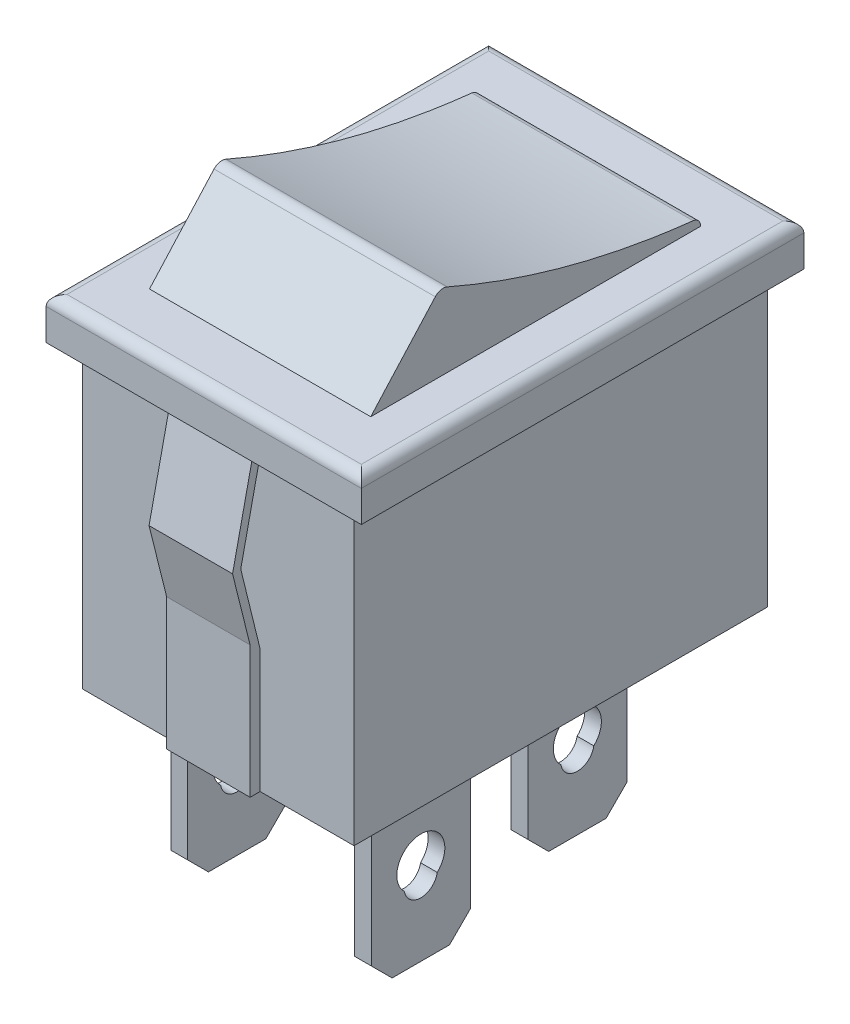
SolidWorks part; units mm, degrees
ref_plane "Front Plane" through (0, 0, 0) normal (0, 0, 1) x (1, 0, 0)
ref_plane "Top Plane" through (0, 0, 0) normal (0, 1, 0) x (1, 0, 0)
ref_plane "Right Plane" through (0, 0, 0) normal (1, 0, 0) x (0, 0, -1)
sketch "Sketch1" plane through (0, 0, 0) normal (0, 1, 0) x (1, 0, 0)
  line L1 (-6.5, -9.9) -> (6.5, -9.9)
  line L2 (-6.5, -9.9) -> (-6.5, 9.9)
  line L3 (-6.5, 9.9) -> (6.5, 9.9)
  line L4 (6.5, -9.9) -> (6.5, 9.9)
  line L5 (-6.5, -9.9) -> (6.5, 9.9) construction
  line L6 (-6.5, 9.9) -> (6.5, -9.9) construction
  point P0 (0, 0)
  dimension "D1" = 13
  dimension "D2" = 19.8
extrude "Boss-Extrude1" add sketch "Sketch1" along normal blind 14.2
sketch "Sketch2" plane through (0, 14.2, 0) normal (0, 1, 0) x (1, 0, 0)
  line L1 (-7.55, -10.6) -> (7.55, -10.6)
  line L2 (-7.55, -10.6) -> (-7.55, 10.6)
  line L3 (-7.55, 10.6) -> (7.55, 10.6)
  line L4 (7.55, -10.6) -> (7.55, 10.6)
  line L5 (-7.55, -10.6) -> (7.55, 10.6) construction
  line L6 (-7.55, 10.6) -> (7.55, -10.6) construction
  point P0 (0, 0)
  dimension "D1" = 21.2
  dimension "D2" = 15.1
extrude "Boss-Extrude2" add sketch "Sketch2" along normal blind 2
fillet "Fillet1" radius 0.5 4 edges at (0, 16.2, 10.6) (-7.55, 16.2, 0) (0, 16.2, -10.6) (7.55, 16.2, 0)
sketch "Sketch3" plane through (0, 16.2, 0) normal (0, 1, 0) x (1, 0, 0)
  line L1 (-5.3, -7.9) -> (5.3, -7.9)
  line L2 (-5.3, -7.9) -> (-5.3, 7.9)
  line L3 (-5.3, 7.9) -> (5.3, 7.9)
  line L4 (5.3, -7.9) -> (5.3, 7.9)
  line L5 (-5.3, -7.9) -> (5.3, 7.9) construction
  line L6 (-5.3, 7.9) -> (5.3, -7.9) construction
  point P0 (0, 0)
  dimension "D1" = 15.8
  dimension "D2" = 10.6
extrude "Boss-Extrude3" add sketch "Sketch3" along normal blind 3.7
sketch "Sketch4" plane through (5.3, 0, 0) normal (1, 0, 0) x (0, 0, -1)
  line L1 (-7.9, 19.9) -> (7.9, 19.9) construction
  line L2 (7.9, 19.9) -> (7.9, 16.2) construction
  line L3 (-7.9, 16.2) -> (-4.5639, 19.9)
  spline S0 degree 2 poles (-4.5639, 19.9) (1.4036, 17.2189) (7.9, 16.5741) knots 0 0 0 1 1 1
  line M4 (7.9, 16.2) -> (7.9, 19.9)
  line M5 (7.9, 19.9) -> (-7.9, 19.9)
  line M6 (-7.9, 19.9) -> (-7.9, 16.2)
  dimension "D1" = 12.9
extrude "Cut-Extrude1" cut sketch "Sketch4" against normal through all and the other way through all contours L3 M6 M5 | S0 M5 M4
fillet "Fillet2" radius 0.5 1 edges at (0, 19.9, 4.5639)
fillet "Fillet3" radius 0.4 1 edges at (0, 16.5741, -7.9)
sketch "Sketch8" plane through (0, 0, 0) normal (1, 0, 0) x (0, 0, -1)
  line L0 (0, 5.9179) -> (0, -5.9179) construction
  line L1 (-9.9, 13.9348) -> (-10.2909, 13.9348)
  line L2 (-10.8274, 9.693) -> (-9.9, 13.9348)
  line L3 (-9.9, 5.9179) -> (-10.8274, 9.693)
  line L4 (10.379, 0) -> (10.379, 6.3212)
  line L5 (-11.2202, 9.693) -> (-10.2909, 13.9348)
  line L7 (9.9, 5.9179) -> (9.9, 0)
  line L8 (9.9, 14.2) -> (9.9, 0) construction
  line L9 (-10.379, 6.3212) -> (-11.2202, 9.693)
  line L10 (9.9, 0) -> (10.379, 0)
  line L11 (10.379, 6.3212) -> (11.2202, 9.693)
  line L12 (11.2202, 9.693) -> (10.2909, 13.9348)
  line L13 (9.9, 5.9179) -> (10.8274, 9.693)
  line L14 (10.8274, 9.693) -> (9.9, 13.9348)
  line L15 (9.9, 13.9348) -> (10.2909, 13.9348)
  line L16 (-9.9, 0) -> (-10.379, 0)
  line L17 (-9.9, 5.9179) -> (-9.9, 0)
  line L18 (-10.379, 0) -> (-10.379, 6.3212)
extrude "Boss-Extrude4" add sketch "Sketch8" along normal blind 2 and the other way blind 2 separate body
sketch "Sketch9" plane through (0, 0, 0) normal (0, -1, 0) x (1, 0, 0)
  line L0 (0, 9.9) -> (0, -9.9) construction
  line L1 (-4.8, 7.375) -> (-4, 7.375)
  line L2 (-4.8, 7.375) -> (-4.8, 2.625)
  line L3 (-4.8, 2.625) -> (-4, 2.625)
  line L4 (-4, 7.375) -> (-4, 2.625)
  line L5 (-3.3, -1.625) -> (-2.5, -1.625)
  line L6 (-3.3, -1.625) -> (-3.3, -6.375)
  line L7 (-3.3, -6.375) -> (-2.5, -6.375)
  line L8 (-2.5, -1.625) -> (-2.5, -6.375)
  line L9 (-6.5, 9.9) -> (6.5, 9.9) construction
  line L10 (-2, -9.9) -> (2, -9.9) construction
  line L11 (2.5, -1.625) -> (2.5, -6.375)
  line L12 (3.3, -6.375) -> (2.5, -6.375)
  line L13 (3.3, -1.625) -> (3.3, -6.375)
  line L14 (3.3, -1.625) -> (2.5, -1.625)
  line L15 (4, 7.375) -> (4, 2.625)
  line L16 (4.8, 2.625) -> (4, 2.625)
  line L17 (4.8, 7.375) -> (4.8, 2.625)
  line L18 (4.8, 7.375) -> (4, 7.375)
  line L19 (0, 0) -> (3.3, 0) construction
  line L20 (-4, 5) -> (4, 5) construction
  line L21 (-2.5, -4) -> (2.5, -4) construction
  dimension "D1" = 0.8
  dimension "D2" = 4.75
  dimension "D3" = 4.75
  dimension "D4" = 0.8
  dimension "D5" = 4
  dimension "D6" = 2.5
  dimension "D7" = 5
  dimension "D8" = 4
extrude "Boss-Extrude5" add sketch "Sketch9" along normal blind 8.1
chamfer "Chamfer1" distance 1 angle 45 8 edges at (-2.9, -8.1, -1.625) (-2.9, -8.1, -6.375) (2.9, -8.1, -6.375) (2.9, -8.1, -1.625) (4.4, -8.1, 2.625) (4.4, -8.1, 7.375) (-4.4, -8.1, 2.625) (-4.4, -8.1, 7.375)
sketch "Sketch10" plane through (4.8, 0, 0) normal (1, 0, 0) x (0, 0, -1)
  line L0 (0, 0) -> (0, -2.5809) construction
  arc A0 (-4.2119, -4.7986) -> (-5.7881, -4.7986) centre (-5, -3.9611) ccw
  arc A1 (-5.7881, -4.7986) -> (-4.2119, -4.7986) centre (-5, -4.6611) ccw
  arc A2 (4.7881, -4.7986) -> (3.2119, -4.7986) centre (4, -3.9611) ccw
  arc A3 (3.2119, -4.7986) -> (4.7881, -4.7986) centre (4, -4.6611) ccw
  dimension "D1" = 2.3
  dimension "D2" = 1.6
  dimension "D3" = 2.65
  dimension "D4" = 5
  dimension "D5" = 4
extrude "Cut-Extrude2" cut sketch "Sketch10" against normal through all
